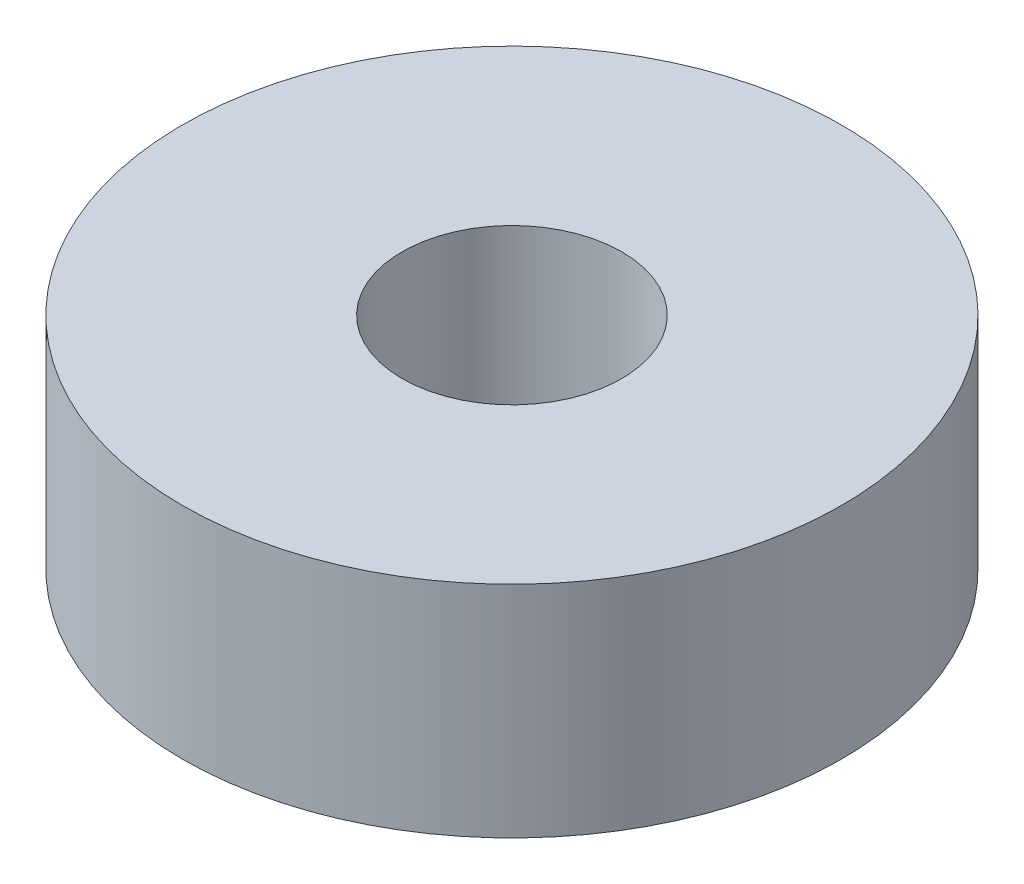
SolidWorks part; units mm, degrees
ref_plane "Front" through (0, 0, 0) normal (0, 0, 1) x (1, 0, 0)
ref_plane "Top" through (0, 0, 0) normal (0, 1, 0) x (1, 0, 0)
ref_plane "Right" through (0, 0, 0) normal (1, 0, 0) x (0, 0, -1)
sketch "Sketch1" plane through (0, 0, 0) normal (0, 1, 0) x (1, 0, 0)
  circle A0 centre (0, 0) radius 4.5
  circle A1 centre (0, 0) radius 1.5
  dimension "D1" = 9
  dimension "D2" = 3
extrude "Boss-Extrude1" add sketch "Sketch1" along normal blind 3
